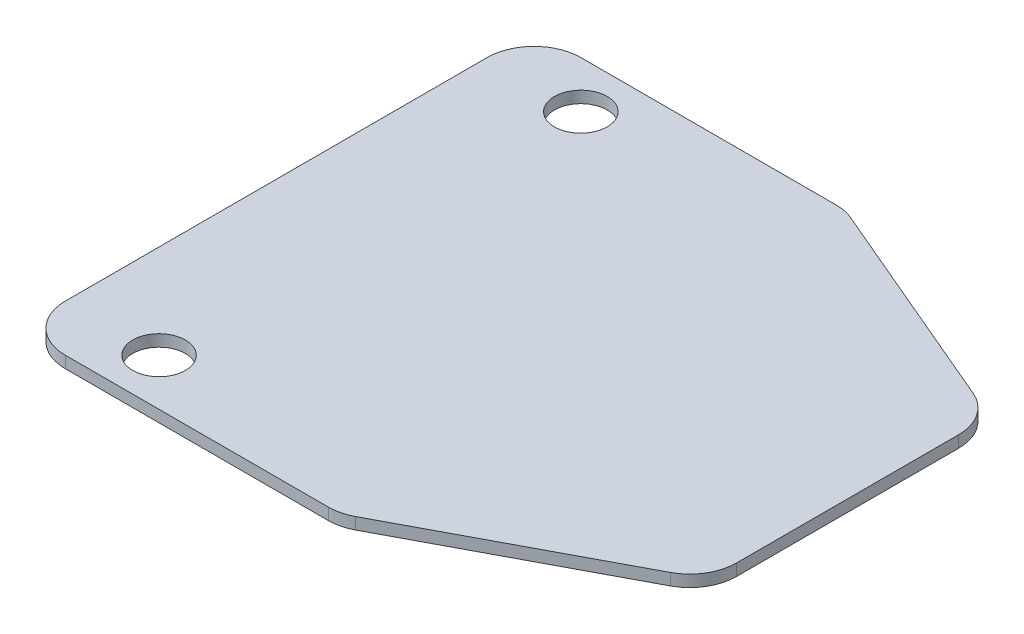
SolidWorks part; units mm, degrees
ref_plane "Front Plane" through (0, 0, 0) normal (0, 0, 1) x (1, 0, 0)
ref_plane "Top Plane" through (0, 0, 0) normal (0, 1, 0) x (1, 0, 0)
ref_plane "Right Plane" through (0, 0, 0) normal (1, 0, 0) x (0, 0, -1)
sketch "Sketch1" plane through (0, 0, 0) normal (0, 1, 0) x (1, 0, 0)
  line L0 (-125.8162, -9.9122) -> (4.7599, 59.2252)
  line L1 (-300.0401, 269.4878) -> (-131.1886, 269.4878)
  line L2 (-300.0401, 269.4878) -> (-300.0401, -9.9122)
  line L3 (-300.0401, -9.9122) -> (-125.8162, -9.9122)
  line L4 (4.7599, 211.6252) -> (4.7599, 59.2252)
  line L5 (-131.1886, 269.4878) -> (4.7599, 211.6252)
  circle A4 centre (-249.2401, 244.0878) radius 14.2875
  circle A5 centre (-249.2401, 15.4878) radius 14.2875
  point P0 (-300.0401, 269.6359)
  point P1 (-302.2475, -9.8295)
  point P2 (-302.6641, -10.166)
  point P11 (-300.0401, -9.9122)
  point P14 (-300.0401, 269.4878)
  point P19 (-125.8162, -9.9122)
  point P20 (-131.1886, 269.4878)
  point P21 (-125.8162, -9.9122)
  point P24 (4.7599, 211.6252)
  point P25 (4.7599, 59.2252)
  point P26 (4.7599, 135.4252)
  point P27 (4.7599, 211.6252)
  point P28 (4.7599, 135.4252)
  dimension "D3" = 147.7501
  dimension "D4" = 28.575
  dimension "D5" = 28.575
  dimension "D2" = 279.4
  dimension "D6" = 50.8
  dimension "D7" = 25.4
  dimension "D8" = 50.8
  dimension "D9" = 25.4
  dimension "D10" = 147.7501
  dimension "D11" = 168.8515
  dimension "D12" = 152.4
  dimension "D13" = 304.8
extrude "Boss-Extrude4" add sketch "Sketch1" along normal blind 6.35
fillet "Fillet3" radius 25.4 6 edges at (4.7599, 3.175, -211.6252) (-131.1886, 3.175, -269.4878) (-300.0401, 3.175, -269.4878) (4.7599, 3.175, -59.2252) (-125.8162, 3.175, 9.9122) (-300.0401, 3.175, 9.9122)
